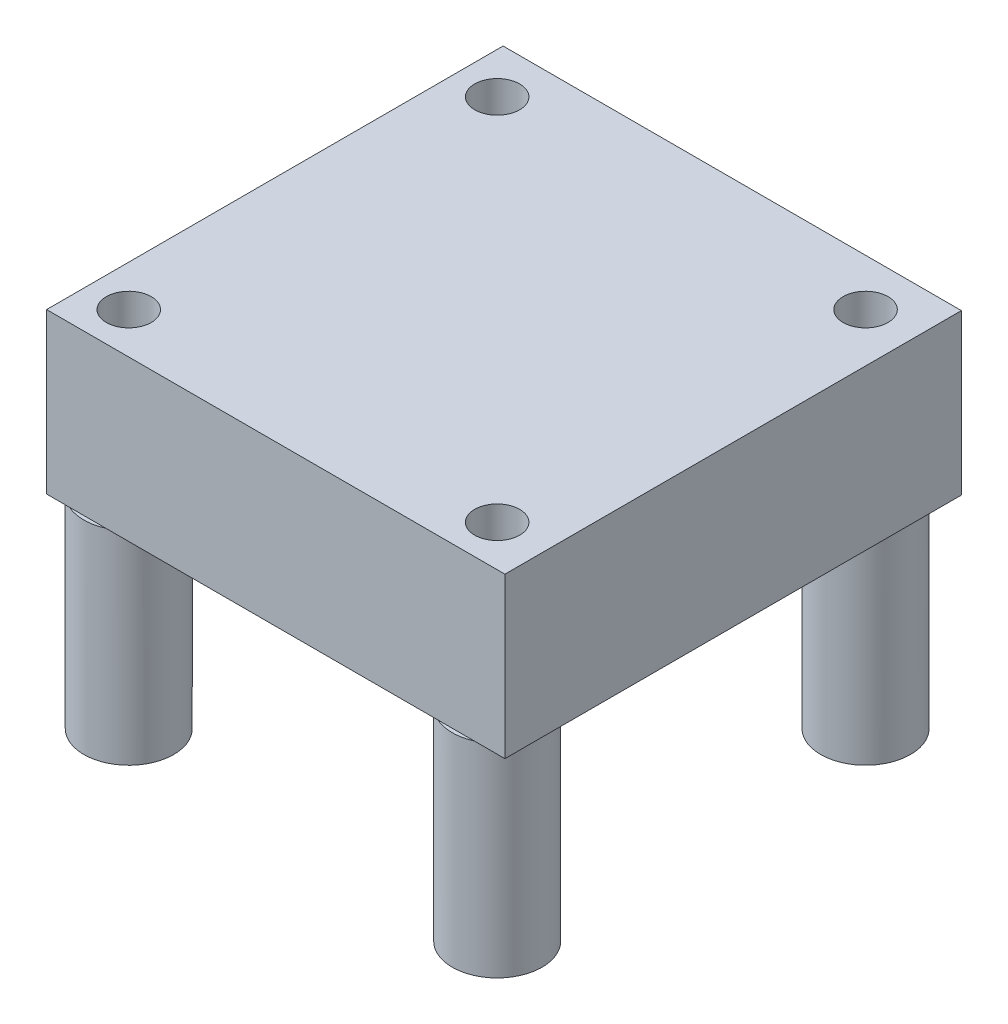
SolidWorks part; units mm, degrees
ref_plane "Front Plane" through (0, 0, 0) normal (0, 0, 1) x (1, 0, 0)
ref_plane "Top Plane" through (0, 0, 0) normal (0, 1, 0) x (1, 0, 0)
ref_plane "Right Plane" through (0, 0, 0) normal (1, 0, 0) x (0, 0, -1)
sketch "Sketch1" plane through (0, 0, 0) normal (0, 1, 0) x (1, 0, 0)
  line L1 (-16.8639, 11.4761) -> (8.6361, 11.4761)
  line L2 (-16.8639, 11.4761) -> (-16.8639, -13.9239)
  line L3 (-16.8639, -13.9239) -> (8.6361, -13.9239)
  line L4 (8.6361, 11.4761) -> (8.6361, -13.9239)
  dimension "D1" = 25.4
  dimension "D2" = 25.5
extrude "Boss-Extrude1" add sketch "Sketch1" along normal blind 8.89
sketch "Sketch2" plane through (0, 0, 0) normal (0, -1, 0) x (1, 0, 0)
  circle A0 centre (-14.5779, 11.6379) radius 2.5
  circle A1 centre (5.9199, 11.6379) radius 2.5
  circle A2 centre (5.9199, -8.8599) radius 2.5
  circle A3 centre (-14.5779, -8.8599) radius 2.5
  dimension "D1" = 5
  dimension "D3" = 20.4978
  dimension "D6" = 5
  dimension ".2" = 5
  dimension "D12" = 5
  dimension "D2" = 20.4978
extrude "Boss-Extrude2" add sketch "Sketch2" along normal blind 11.303
sketch "Sketch3" plane through (0, -11.303, 0) normal (0, -1, 0) x (1, 0, 0)
  circle A0 centre (-14.5779, 11.6379) radius 1.25
  circle A1 centre (-14.5779, -8.8599) radius 1.25
  circle A2 centre (5.9199, -8.8599) radius 1.25
  circle A3 centre (5.9199, 11.6379) radius 1.25
  dimension "D1" = 2.5
  dimension "D2" = 2.5
  dimension "D3" = 2.5
  dimension "D4" = 2.5
extrude "Cut-Extrude1" cut sketch "Sketch3" against normal through all
